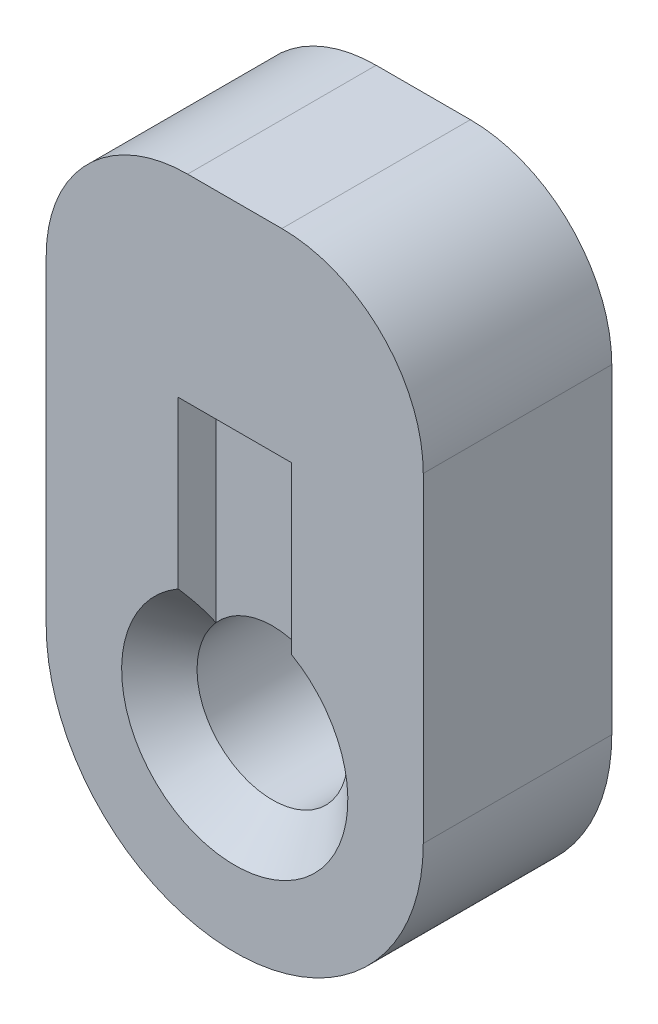
SolidWorks part; units mm, degrees
ref_plane "Front Plane" through (0, 0, 0) normal (0, 0, 1) x (1, 0, 0)
ref_plane "Top Plane" through (0, 0, 0) normal (0, 1, 0) x (1, 0, 0)
ref_plane "Right Plane" through (0, 0, 0) normal (1, 0, 0) x (0, 0, -1)
sketch "Sketch2" plane through (0, 0, 0) normal (0, 0, 1) x (1, 0, 0)
  line L5 (-0.762, 0) -> (0.762, 0)
  line L6 (-2.54, 0) -> (2.54, 0)
  line L13 (-2.54, 0) -> (-2.54, 4.318)
  line L14 (-0.635, 6.223) -> (0.635, 6.223)
  line L15 (2.54, 0) -> (2.54, 4.318)
  line L16 (-0.762, 0) -> (-0.762, 3.556)
  line L17 (-0.762, 3.556) -> (0.762, 3.556)
  line L18 (0.762, 0) -> (0.762, 3.556)
  circle A0 centre (0, 0) radius 1.524
  circle A1 centre (0, 0) radius 1.016
  circle A2 centre (0, 0) radius 2.54
  arc A3 (2.54, 4.318) -> (0.635, 6.223) centre (0.635, 4.318) ccw
  arc A4 (-2.54, 4.318) -> (-0.635, 6.223) centre (-0.635, 4.318) cw
  point P0 (0, 0)
  point P5 (0, 0)
  dimension "D1" = 2.032
  dimension "D2" = 3.048
  dimension "D5" = 5.08
  dimension "D7" = 1.905
  dimension "D3" = 1.524
  dimension "D4" = 3.556
  dimension "D6" = 6.223
extrude "Boss-Extrude2" add sketch "Sketch2" along normal blind 2.54 contours L6 A2 A0 | A1 L6 A0 | A1 L6 A0 L18 | A1 L18 A0 L16 | A1 L16 A0 L6 | L16 A2 L6 A0 | L18 A2 L16 A0 | L6 A2 L18 A0 | A2 L15 L14 L13 L16 L17 L18 | A2 L18 L17 L16
sketch "Sketch3" plane through (0, 0, 2.54) normal (0, 0, 1) x (1, 0, 0)
  line L4 (-2.54, 0) -> (2.54, 0)
  line L5 (-2.54, 4.318) -> (-2.54, 0)
  line L6 (0.635, 6.223) -> (-0.635, 6.223)
  line L7 (2.54, 0) -> (2.54, 4.318)
  line L8 (-2.54, 0) -> (2.54, 0)
  line L9 (-2.54, 4.318) -> (-2.54, 0)
  line L10 (0.635, 6.223) -> (-0.635, 6.223)
  line L11 (2.54, 0) -> (2.54, 4.318)
  line L12 (-0.762, 0) -> (0.762, 0)
  line L13 (-0.762, 3.556) -> (-0.762, 0)
  line L14 (0.762, 3.556) -> (-0.762, 3.556)
  line L15 (0.762, 0) -> (0.762, 3.556)
  line L16 (-0.762, 0) -> (0.762, 0)
  line L17 (-0.762, 3.556) -> (-0.762, 0)
  line L18 (0.762, 3.556) -> (-0.762, 3.556)
  line L19 (0.762, 0) -> (0.762, 3.556)
  circle A1 centre (0, 0) radius 2.54
  circle A2 centre (0, 0) radius 2.54
  circle A3 centre (0, 0) radius 1.016
  circle A4 centre (0, 0) radius 1.016
  circle A5 centre (0, 0) radius 1.524
  circle A6 centre (0, 0) radius 1.524
  arc A8 (2.54, 4.318) -> (0.635, 6.223) centre (0.635, 4.318) ccw
  arc A9 (2.54, 4.318) -> (0.635, 6.223) centre (0.635, 4.318) ccw
  arc A10 (-0.635, 6.223) -> (-2.54, 4.318) centre (-0.635, 4.318) ccw
  arc A11 (-0.635, 6.223) -> (-2.54, 4.318) centre (-0.635, 4.318) ccw
  circle M16 centre (0, 0) radius 1.016
  dimension "D1" = 0
  dimension "D2" = 0
  dimension "D3" = 0
  dimension "D4" = 0
  dimension "D5" = 0
extrude "Cut-Extrude1" cut sketch "Sketch3" against normal blind 0.508 contours A6 L19 A2 L17 | A2 L19 L18 L17 | L19 A6 L17 M16
sketch "Sketch4" plane through (0, 0, 0) normal (0, 0, -1) x (-1, 0, 0)
  line L3 (2.54, 0) -> (2.54, 4.318)
  line L4 (0.635, 6.223) -> (-0.635, 6.223)
  line L5 (-2.54, 4.318) -> (-2.54, 0)
  line L6 (2.54, 0) -> (2.54, 4.318)
  line L7 (0.635, 6.223) -> (-0.635, 6.223)
  line L8 (-2.54, 4.318) -> (-2.54, 0)
  line L10 (-2.54, 0) -> (2.54, 0)
  line L11 (2.54, 0) -> (2.54, 4.318)
  line L12 (0.635, 6.223) -> (-0.635, 6.223)
  line L13 (-2.54, 4.318) -> (-2.54, 0)
  line L14 (-2.54, 0) -> (2.54, 0)
  line L15 (2.54, 0) -> (2.54, 4.318)
  line L16 (0.635, 6.223) -> (-0.635, 6.223)
  line L17 (-2.54, 4.318) -> (-2.54, 0)
  line L18 (-0.762, 0) -> (0.762, 0)
  line L19 (0.762, 0) -> (0.762, 3.556)
  line L20 (0.762, 3.556) -> (-0.762, 3.556)
  line L21 (-0.762, 3.556) -> (-0.762, 0)
  line L22 (-0.762, 0) -> (0.762, 0)
  line L23 (0.762, 0) -> (0.762, 3.556)
  line L24 (0.762, 3.556) -> (-0.762, 3.556)
  line L25 (-0.762, 3.556) -> (-0.762, 0)
  arc A1 (-2.54, 0) -> (2.54, 0) centre (0, 0) ccw
  arc A2 (-2.54, 0) -> (2.54, 0) centre (0, 0) ccw
  circle A3 centre (0, 0) radius 2.54
  circle A4 centre (0, 0) radius 2.54
  circle A5 centre (0, 0) radius 1.016
  circle A6 centre (0, 0) radius 1.016
  circle A7 centre (0, 0) radius 1.524
  circle A8 centre (0, 0) radius 1.524
  arc A10 (-0.635, 6.223) -> (-2.54, 4.318) centre (-0.635, 4.318) ccw
  arc A11 (2.54, 4.318) -> (0.635, 6.223) centre (0.635, 4.318) ccw
  arc A12 (2.54, 4.318) -> (0.635, 6.223) centre (0.635, 4.318) ccw
  arc A13 (-0.635, 6.223) -> (-2.54, 4.318) centre (-0.635, 4.318) ccw
  arc A14 (-0.635, 6.223) -> (-2.54, 4.318) centre (-0.635, 4.318) ccw
  arc A15 (-0.635, 6.223) -> (-2.54, 4.318) centre (-0.635, 4.318) ccw
  arc A16 (2.54, 4.318) -> (0.635, 6.223) centre (0.635, 4.318) ccw
  arc A17 (2.54, 4.318) -> (0.635, 6.223) centre (0.635, 4.318) ccw
  circle M20 centre (0, 0) radius 1.016
  dimension "D1" = 0
  dimension "D2" = 0
  dimension "D3" = 0
  dimension "D4" = 0
  dimension "D5" = 0
  dimension "D6" = 0
extrude "Cut-Extrude2" cut sketch "Sketch4" against normal blind 0.508 contours A4 L23 L24 L25 | A8 L23 A4 L25 | L23 A8 L25 M20
sketch "Sketch7" plane through (0, 0, 0) normal (0, 1, 0) x (1, 0, 0)
  line L0 (0, 0) -> (0, -2.54)
  line L1 (-0.635, -2.54) -> (0.635, -2.54) construction
  line L2 (0, -2.54) -> (1.524, -2.54)
  line L3 (1.524, -2.54) -> (0.508, -1.524)
  line L4 (0.508, -1.524) -> (0.508, -1.016)
  line L5 (0.508, -1.016) -> (1.524, 0)
  line L6 (-0.635, 0) -> (0.635, 0) construction
  line L7 (1.524, 0) -> (0, 0)
  point P5 (0.508, -1.27)
  point P12 (0, -1.27)
  dimension "D1" = 0.508
  dimension "D2" = 45
  dimension "D4" = 1.524
revolve "Cut-Revolve1" cut sketch "Sketch7" angle 360 about L0
